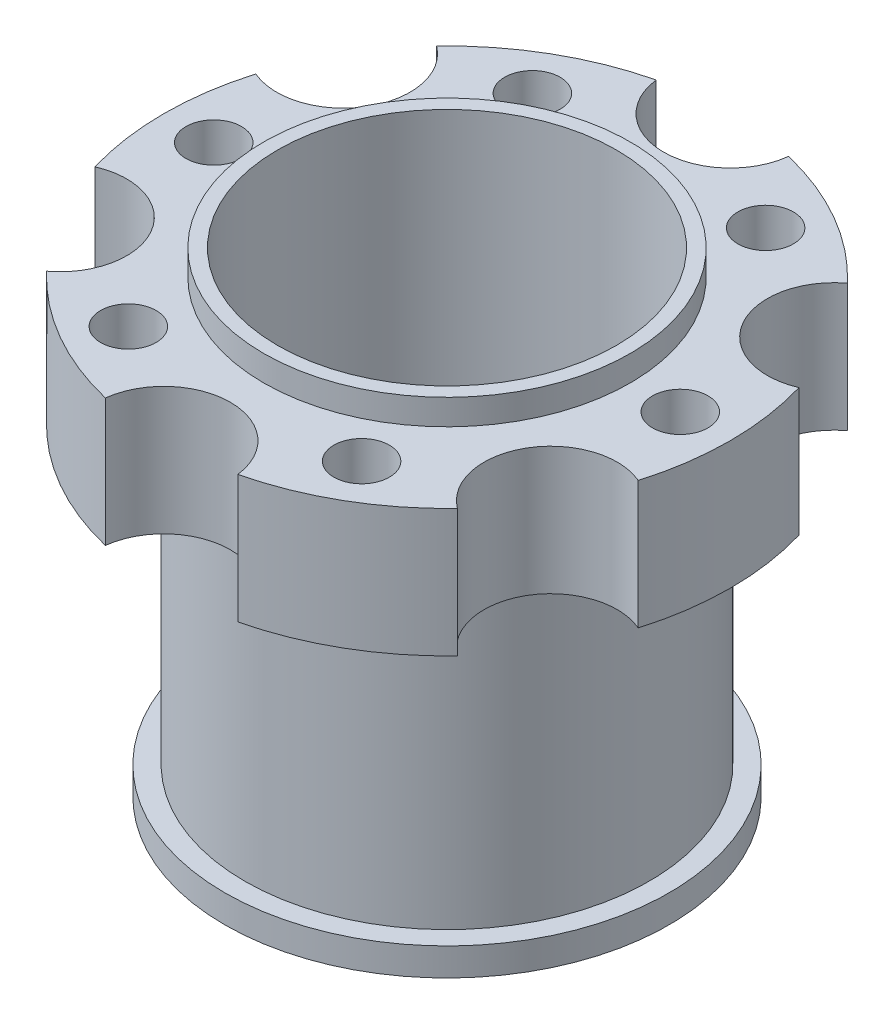
SolidWorks part; units mm, degrees
material "1.4306 (X2CrNi19-11)"
ref_plane "正面" through (0, 0, 0) normal (0, 0, 1) x (1, 0, 0)
ref_plane "平面" through (0, 0, 0) normal (0, 1, 0) x (1, 0, 0)
ref_plane "右側面" through (0, 0, 0) normal (1, 0, 0) x (0, 0, -1)
sketch "ｽｹｯﾁ1" plane through (0, 0, 0) normal (0, 1, 0) x (1, 0, 0)
  line L0 (0, 0) -> (0, 25.5) construction
  arc A0 (-5.9583, 24.7941) -> (5.9583, 24.7941) centre (0, 0) cw
  arc A1 (-5.9583, 24.7941) -> (5.9583, 24.7941) centre (0, 25.5) ccw
  arc A2 (18.4932, 17.5571) -> (24.4515, 7.237) centre (22.0836, 12.75) ccw
  arc A3 (18.4932, 17.5571) -> (24.4515, 7.237) centre (0, 0) cw
  arc A4 (24.4515, -7.237) -> (18.4932, -17.5571) centre (22.0836, -12.75) ccw
  arc A5 (24.4515, -7.237) -> (18.4932, -17.5571) centre (0, 0) cw
  arc A6 (5.9583, -24.7941) -> (-5.9583, -24.7941) centre (0, -25.5) ccw
  arc A7 (5.9583, -24.7941) -> (-5.9583, -24.7941) centre (0, 0) cw
  arc A8 (-18.4932, -17.5571) -> (-24.4515, -7.237) centre (-22.0836, -12.75) ccw
  arc A9 (-18.4932, -17.5571) -> (-24.4515, -7.237) centre (0, 0) cw
  arc A10 (-24.4515, 7.237) -> (-18.4932, 17.5571) centre (-22.0836, 12.75) ccw
  arc A11 (-24.4515, 7.237) -> (-18.4932, 17.5571) centre (0, 0) cw
  arc A12 (5.9583, 24.7941) -> (18.4932, 17.5571) centre (0, 0) cw
  arc A13 (24.4515, 7.237) -> (24.4515, -7.237) centre (0, 0) cw
  arc A14 (18.4932, -17.5571) -> (5.9583, -24.7941) centre (0, 0) cw
  arc A15 (-5.9583, -24.7941) -> (-18.4932, -17.5571) centre (0, 0) cw
  arc A16 (-24.4515, -7.237) -> (-24.4515, 7.237) centre (0, 0) cw
  arc A17 (-18.4932, 17.5571) -> (-5.9583, 24.7941) centre (0, 0) cw
  point P28 (0, 0)
  point P35 (0, 0)
  dimension "D1" = 6
  dimension "D2" = 6
extrude "ﾎﾞｽ - 押し出し1" add sketch "ｽｹｯﾁ1" along normal blind 11.5
sketch "ｽｹｯﾁ2" plane through (0, 11.5, 0) normal (0, 1, 0) x (1, 0, 0)
  circle A0 centre (0, 0) radius 16.5
  circle A1 centre (0, 0) radius 15.25
  dimension "D1" = 33
  dimension "D2" = 30.5
extrude "ﾎﾞｽ - 押し出し2" add sketch "ｽｹｯﾁ2" along normal blind 2.3
sketch "ｽｹｯﾁ3" plane through (0, 11.5, 0) normal (0, 1, 0) x (1, 0, 0)
  circle A0 centre (0, 0) radius 15.25
extrude "ｶｯﾄ - 押し出し2" cut sketch "ｽｹｯﾁ3" against normal through all
sketch "ｽｹｯﾁ4" plane through (0, 0, 0) normal (0, -1, 0) x (1, 0, 0)
  circle A0 centre (0, 0) radius 18.2
  circle A1 centre (0, 0) radius 15.25
  dimension "D1" = 36.4
extrude "ﾎﾞｽ - 押し出し3" add sketch "ｽｹｯﾁ4" along normal blind 26.5
sketch "ｽｹｯﾁ5" plane through (0, -26.5, 0) normal (0, -1, 0) x (1, 0, 0)
  circle A0 centre (0, 0) radius 20
  circle A1 centre (0, 0) radius 18.2
  dimension "D1" = 40
extrude "ﾎﾞｽ - 押し出し4" add sketch "ｽｹｯﾁ5" along normal blind 2.5 separate body
sketch "ｽｹｯﾁ6" plane through (0, -26.5, 0) normal (0, -1, 0) x (1, 0, 0)
  circle A0 centre (0, 0) radius 18.2
  circle A1 centre (0, 0) radius 15.25
sketch "ｽｹｯﾁ7" plane through (0, 11.5, 0) normal (0, 1, 0) x (1, 0, 0)
  circle A0 centre (21, 0) radius 2.5
  circle A1 centre (10.5, -18.1865) radius 2.5
  circle A2 centre (-10.5, -18.1865) radius 2.5
  circle A3 centre (-21, 0) radius 2.5
  circle A4 centre (-10.5, 18.1865) radius 2.5
  circle A5 centre (10.5, 18.1865) radius 2.5
  point P15 (0, 0)
  dimension "D1" = 6
extrude "ｶｯﾄ - 押し出し4" cut sketch "ｽｹｯﾁ7" against normal blind 19
